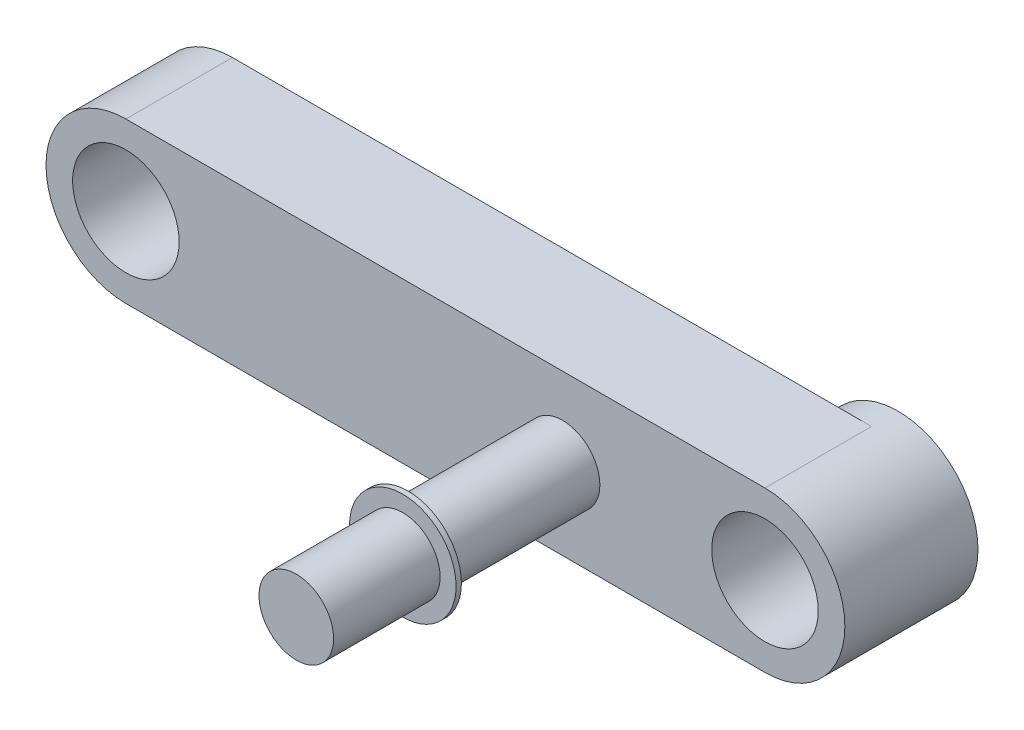
SolidWorks part; units mm, degrees
material "普通碳钢"
ref_plane "前视基准面" through (0, 0, 0) normal (0, 0, 1) x (1, 0, 0)
ref_plane "上视基准面" through (0, 0, 0) normal (0, 1, 0) x (1, 0, 0)
ref_plane "右视基准面" through (0, 0, 0) normal (1, 0, 0) x (0, 0, -1)
sketch "草图1" plane through (0, 0, 0) normal (0, 0, 1) x (1, 0, 0)
  line L0 (0, 0) -> (-12, 0) construction
  line L1 (0, -1.5) -> (-12, -1.5)
  line L2 (0, 1.5) -> (-12, 1.5)
  arc A0 (0, -1.5) -> (0, 1.5) centre (0, 0) ccw
  arc A1 (-12, 1.5) -> (-12, -1.5) centre (-12, 0) ccw
  circle A2 centre (-12, 0) radius 1
  circle A3 centre (0, 0) radius 1
  point P3 (-6, 0)
  dimension "D1" = 1.5
  dimension "D2" = 2
  dimension "D3" = 12
extrude "凸台-拉伸1" add sketch "草图1" along normal blind 2
sketch "草图2" plane through (0, 0, 0) normal (0, 0, 1) x (1, 0, 0)
  arc A0 (0, -1.5) -> (0, 1.5) centre (0, 0) ccw construction
  circle A1 centre (0, 0) radius 1.5
  circle A2 centre (0, 0) radius 1 construction
  circle A3 centre (0, 0) radius 1
extrude "凸台-拉伸2" add sketch "草图2" against normal blind 0.5
sketch "草图3" plane through (0, 0, 2) normal (0, 0, 1) x (1, 0, 0)
  circle A0 centre (-3.8, 0) radius 0.7
  circle A1 centre (0, 0) radius 1 construction
  dimension "D1" = 3.8
  dimension "D2" = 1.4
extrude "凸台-拉伸3" add sketch "草图3" along normal blind 5
sketch "草图4" plane through (0, 0, 7) normal (0, 0, 1) x (1, 0, 0)
  circle A0 centre (-3.8, 0) radius 1
  dimension "D1" = 2
extrude "凸台-拉伸4" add sketch "草图4" against normal blind 0.1 from offset 2 offset against normal yes
